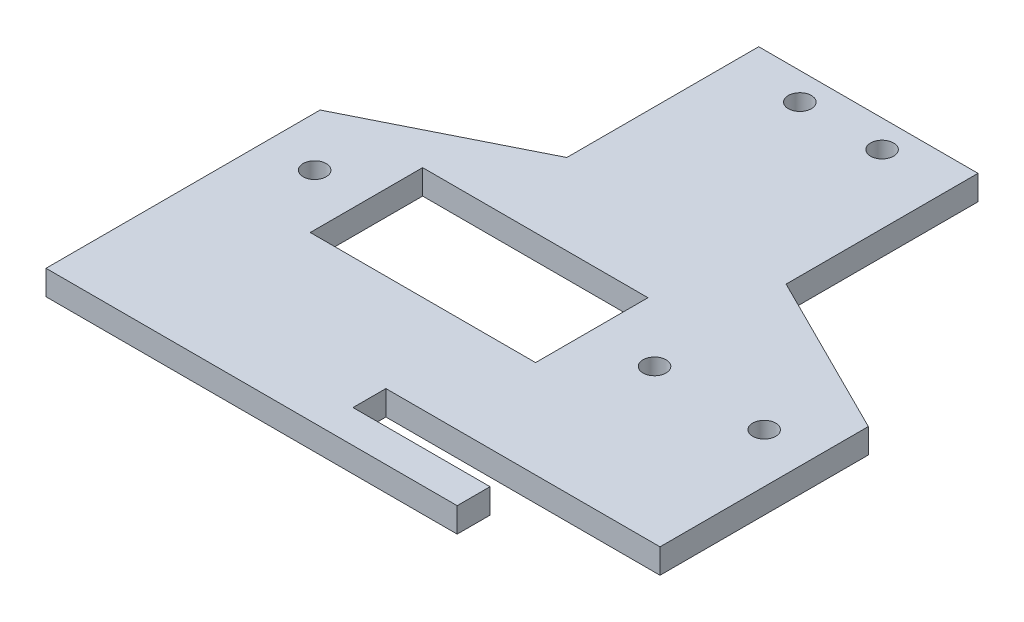
SolidWorks part; units mm, degrees
ref_plane "Front Plane" through (0, 0, 0) normal (0, 0, 1) x (1, 0, 0)
ref_plane "Top Plane" through (0, 0, 0) normal (0, 1, 0) x (1, 0, 0)
ref_plane "Right Plane" through (0, 0, 0) normal (1, 0, 0) x (0, 0, -1)
sketch "Sketch1" plane through (0, 0, 0) normal (0, 1, 0) x (1, 0, 0)
  line L0 (20, 40) -> (50, 25)
  line L1 (-20, 40) -> (-50, 25)
  line L2 (-50, 25) -> (-50, -25)
  line L3 (-50, -25) -> (50, -25)
  line L4 (50, 25) -> (50, -25)
  line L5 (-50, 25) -> (50, -25) construction
  line L6 (-50, -25) -> (50, 25) construction
  line L7 (-20, 40) -> (-20, 75)
  line L8 (-20, 75) -> (20, 75)
  line L9 (20, 75) -> (20, 40)
  circle A0 centre (-41, 15) radius 2.1
  circle A1 centre (41, 15) radius 2.1
  circle A2 centre (-21, 15) radius 2.1
  circle A3 centre (21, 15) radius 2.1
  point P0 (0, 0)
  dimension "D3" = 4.2
  dimension "D4" = 4.2
  dimension "D6" = 20
  dimension "D7" = 4.2
  dimension "D8" = 4.2
  dimension "D1" = 100
  dimension "D2" = 50
  dimension "D5" = 82
  dimension "D9" = 20
  dimension "D10" = 40
  dimension "D11" = 21
  dimension "D12" = 35
extrude "Boss-Extrude1" add sketch "Sketch1" along normal blind 4.5
sketch "Sketch2" plane through (0, 0, 0) normal (0, -1, 0) x (1, 0, 0)
  line L0 (-31.55, -4.75) -> (9.55, -4.75)
  line L1 (9.55, -4.75) -> (9.55, -25.25)
  line L2 (9.55, -25.25) -> (-31.55, -25.25)
  line L3 (-31.55, -25.25) -> (-31.55, -4.75)
  line L9 (-31.3, -24.8) -> (-31.3, -5.2) construction
  line L10 (9.1, -25) -> (-31.1, -25) construction
  line L11 (9.3, -5.2) -> (9.3, -24.8) construction
  dimension "D2" = 0.25
  dimension "D3" = 0.25
  dimension "D4" = 0.25
extrude "Cut-Extrude1" cut sketch "Sketch2" against normal blind 10
sketch "Sketch3" plane through (0, 0, 0) normal (0, -1, 0) x (1, 0, 0)
  line L0 (50, 25) -> (50, -25) construction
  line L1 (0, 19) -> (25, 19)
  line L2 (50, 19) -> (50, 13)
  line L3 (50, 13) -> (0, 13)
  line L4 (0, 19) -> (0, 13)
  line L6 (25, 19) -> (25, 28.7253)
  line L7 (25, 28.7253) -> (50, 28.7253)
  line L8 (50, 28.7253) -> (50, 19)
  dimension "D1" = 25
  dimension "D2" = 6
  dimension "D3" = 50
extrude "Cut-Extrude2" cut sketch "Sketch3" against normal blind 10
sketch "Sketch4" plane through (0, 4.5, 0) normal (0, 1, 0) x (1, 0, 0)
  circle A0 centre (7.5, 70) radius 2.1
  circle A1 centre (-7.5, 70) radius 2.1
  dimension "D1" = 15
  dimension "D2" = 4.2
  dimension "D3" = 4.2
extrude "Cut-Extrude3" cut sketch "Sketch4" against normal blind 10
